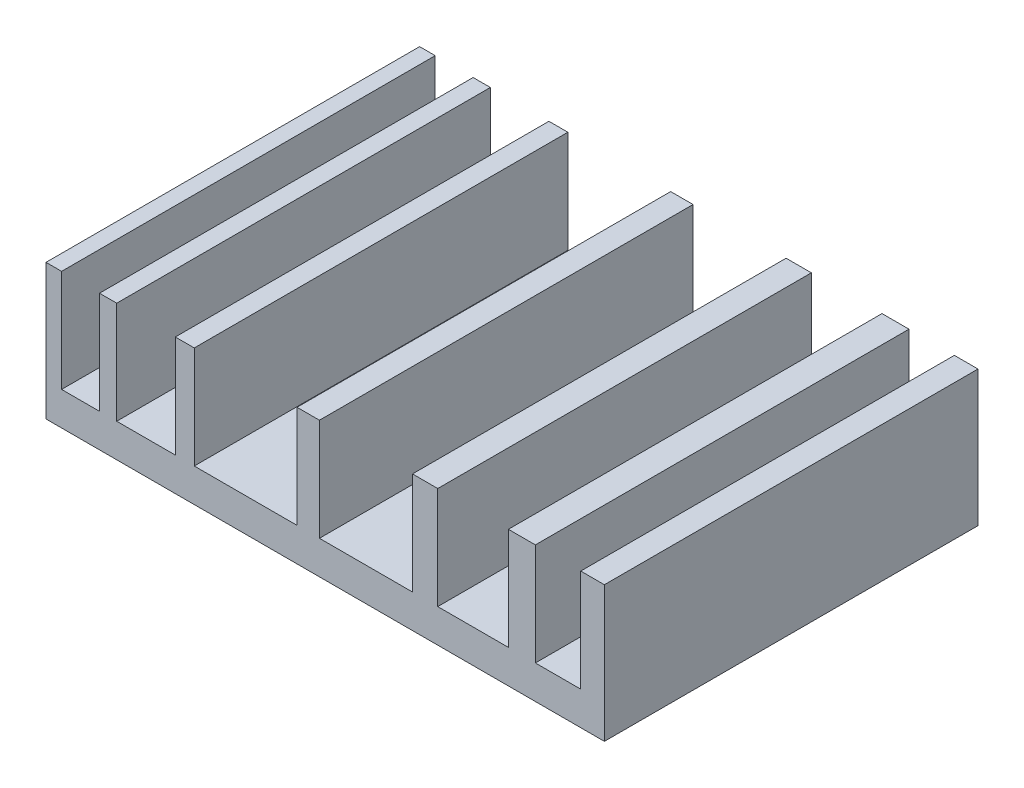
SolidWorks part; units mm, degrees
ref_plane "Front Plane" through (0, 0, 0) normal (0, 0, 1) x (1, 0, 0)
ref_plane "Top Plane" through (0, 0, 0) normal (0, 1, 0) x (1, 0, 0)
ref_plane "Right Plane" through (0, 0, 0) normal (1, 0, 0) x (0, 0, -1)
sketch "Sketch1" plane through (0, 0, 0) normal (0, 1, 0) x (1, 0, 0)
  line L1 (0, 0) -> (81.9, 0)
  line L2 (0, 0) -> (0, 54.8)
  line L3 (0, 54.8) -> (81.9, 54.8)
  line L4 (81.9, 0) -> (81.9, 54.8)
  dimension "D1" = 54.8
  dimension "D2" = 81.9
extrude "Boss-Extrude1" add sketch "Sketch1" along normal blind 19.9
sketch "Sketch3" plane through (0, 19.9, 0) normal (0, 1, 0) x (1, 0, 0)
  line L0 (0, 0) -> (81.9, 0) construction
  line L1 (10.3742, 0) -> (18.9657, 0)
  line L2 (10.3742, 0) -> (10.3742, 54.8)
  line L3 (10.3742, 54.8) -> (18.9657, 54.8)
  line L4 (18.9657, 0) -> (18.9657, 54.8)
  line L5 (81.9, 54.8) -> (0, 54.8) construction
  line L7 (21.7454, 54.8) -> (36.8227, 54.8)
  line L8 (21.7454, 54.8) -> (21.7454, 0)
  line L9 (21.7454, 0) -> (36.8227, 0)
  line L10 (36.8227, 54.8) -> (36.8227, 0)
  line L11 (40.1077, 0) -> (53.7531, 0)
  line L12 (40.1077, 0) -> (40.1077, 54.8)
  line L13 (40.1077, 54.8) -> (53.7531, 54.8)
  line L14 (53.7531, 0) -> (53.7531, 54.8)
  line L15 (57.4593, 54.8) -> (67.8197, 54.8)
  line L16 (57.4593, 54.8) -> (57.4593, 0)
  line L17 (57.4593, 0) -> (67.8197, 0)
  line L18 (67.8197, 54.8) -> (67.8197, 0)
  line L19 (71.7785, 54.8) -> (78.4327, 54.8)
  line L20 (71.7785, 54.8) -> (71.7785, 0)
  line L21 (71.7785, 0) -> (78.4327, 0)
  line L22 (78.4327, 54.8) -> (78.4327, 0)
  line L23 (2.288, 54.8) -> (7.8473, 54.8)
  line L24 (2.288, 54.8) -> (2.288, 0)
  line L25 (2.288, 0) -> (7.8473, 0)
  line L26 (7.8473, 54.8) -> (7.8473, 0)
extrude "Cut-Extrude1" cut sketch "Sketch3" against normal blind 15
